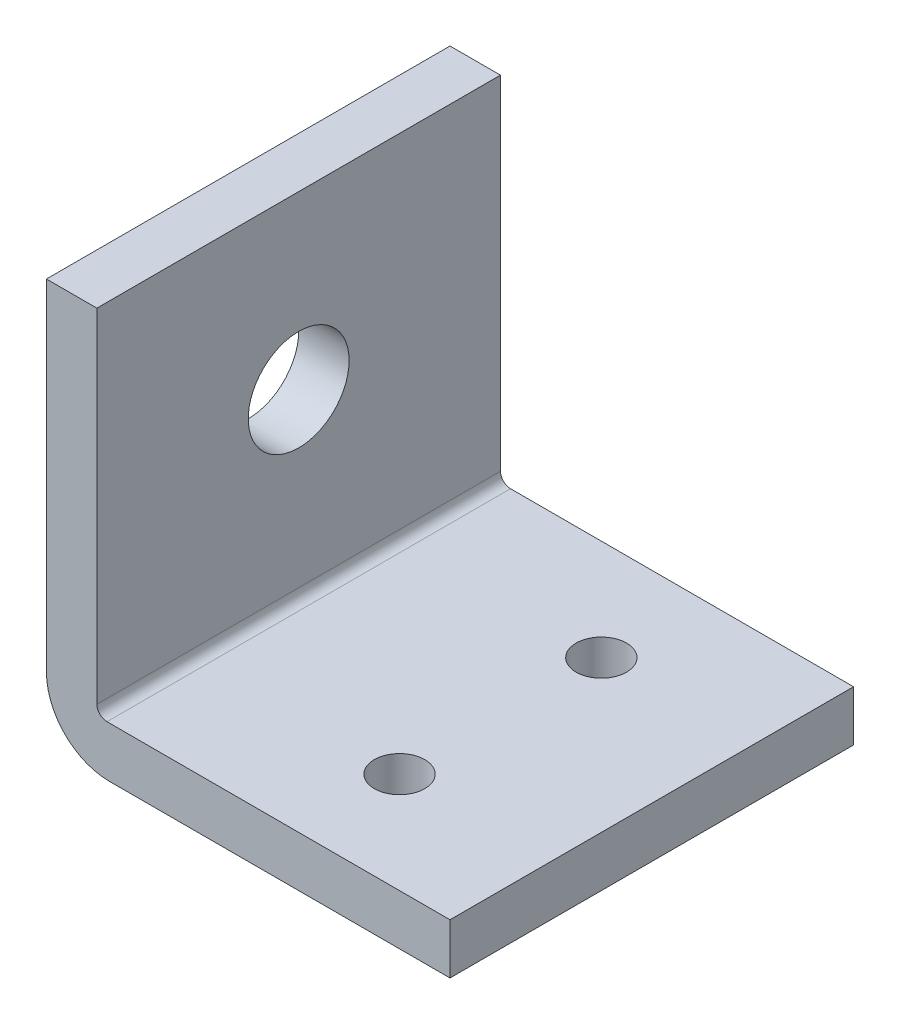
SolidWorks part; units mm, degrees
ref_plane "Front Plane" through (0, 0, 0) normal (0, 0, 1) x (1, 0, 0)
ref_plane "Top Plane" through (0, 0, 0) normal (0, 1, 0) x (1, 0, 0)
ref_plane "Right Plane" through (0, 0, 0) normal (1, 0, 0) x (0, 0, -1)
sketch "Sketch1" plane through (0, 0, 0) normal (0, 1, 0) x (1, 0, 0)
  line L1 (-20, -20) -> (20, -20)
  line L2 (-20, -20) -> (-20, 20)
  line L3 (-20, 20) -> (20, 20)
  line L4 (20, -20) -> (20, 20)
  point P0 (0, 0)
  dimension "D1" = 40
  dimension "D2" = 40
extrude "Boss-Extrude1" add sketch "Sketch1" along normal mid plane 5
sketch "Sketch2" plane through (0, 2.5, 0) normal (0, 1, 0) x (1, 0, 0)
  line L0 (20, 20) -> (-20, 20) construction
  line L1 (-20, -20) -> (-15, -20)
  line L2 (-20, -20) -> (-20, 20)
  line L3 (-20, 20) -> (-15, 20)
  line L4 (-15, -20) -> (-15, 20)
extrude "Boss-Extrude2" add sketch "Sketch2" along normal blind 35
fillet "Fillet2" radius 6.25 1 edges at (-20, -2.5, 0)
fillet "Fillet3" radius 1 1 edges
sketch "Sketch3" plane through (0, 2.5, 0) normal (0, 1, 0) x (1, 0, 0)
  line L2 (20, 20) -> (-14, 20) construction
  circle A0 centre (5, 10) radius 2.5
  circle A1 centre (5, -10) radius 2.5
  dimension "D1" = 15
  dimension "D2" = 10
extrude "Cut-Extrude1" cut sketch "Sketch3" against normal blind 5
sketch "Sketch4" plane through (-15, 0, 0) normal (1, 0, 0) x (0, 0, -1)
  circle A0 centre (0, 20.5) radius 5
extrude "Cut-Extrude2" cut sketch "Sketch4" against normal blind 5
